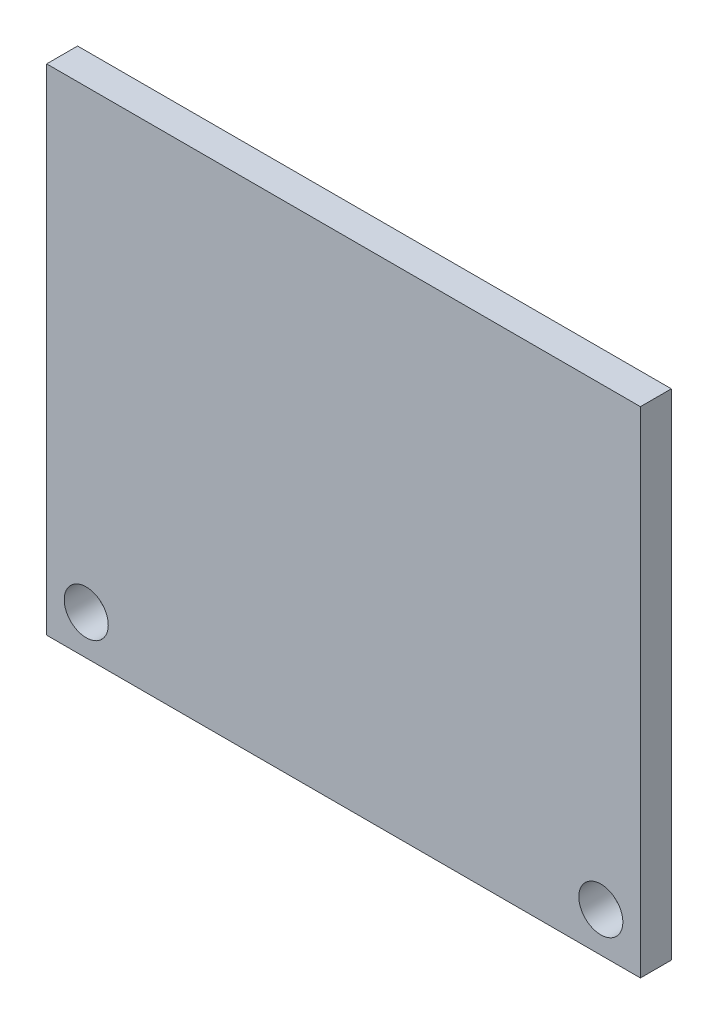
SolidWorks part; units mm, degrees
ref_plane "Front Plane" through (0, 0, 0) normal (0, 0, 1) x (1, 0, 0)
ref_plane "Top Plane" through (0, 0, 0) normal (0, 1, 0) x (1, 0, 0)
ref_plane "Right Plane" through (0, 0, 0) normal (1, 0, 0) x (0, 0, -1)
sketch "Sketch1" plane through (0, 0, 0) normal (0, 0, 1) x (1, 0, 0)
  line L0 (0, 3.9958) -> (0, -6.2934) construction
  line L1 (-15.24, 12.7) -> (15.24, 12.7)
  line L2 (-15.24, 12.7) -> (-15.24, -12.7)
  line L3 (-15.24, -12.7) -> (15.24, -12.7)
  line L4 (15.24, 12.7) -> (15.24, -12.7)
  line L5 (-15.24, 12.7) -> (15.24, -12.7) construction
  line L6 (-15.24, -12.7) -> (15.24, 12.7) construction
  point P0 (0, 0)
  dimension "D1" = 30.48
  dimension "D2" = 25.4
extrude "Boss-Extrude1" add sketch "Sketch1" along normal blind 1.5875
hole_wizard "#2 Clearance Hole1" positions "Sketch4" profile "Sketch3" hole size "#2" standard "Ansi Inch" end condition up to next
sketch "Sketch4" plane through (0, 0, 1.5875) normal (0, 0, 1) x (1, 0, 0)
  line L0 (-15.24, -12.7) -> (15.24, -12.7) construction
  line L1 (-15.24, 12.7) -> (-15.24, -12.7) construction
  point P0 (-13.208, -10.668)
  dimension "D1" = 2.032
  dimension "D2" = 2.032
sketch "Sketch3" plane through (-13.208, -10.668, 1.5875) normal (1, 0, 0) x (0, -1, 0)
  line L0 (0, 0) -> (0, 1.5885)
  line L1 (0, 1.5885) -> (1.1303, 1.5885)
  line L2 (1.1303, 1.5885) -> (1.1303, 0)
  line L5 (1.1303, 0) -> (0, 0)
  line L11 (0, -6.35) -> (0, 107.95) construction
  dimension "Thru Hole Dia." = 2.2606
  dimension "Thru Hole Depth" = 1.5885
mirror "Mirror1" about plane through (0, 0, 0) normal (1, 0, 0) of "#2 Clearance Hole1"
